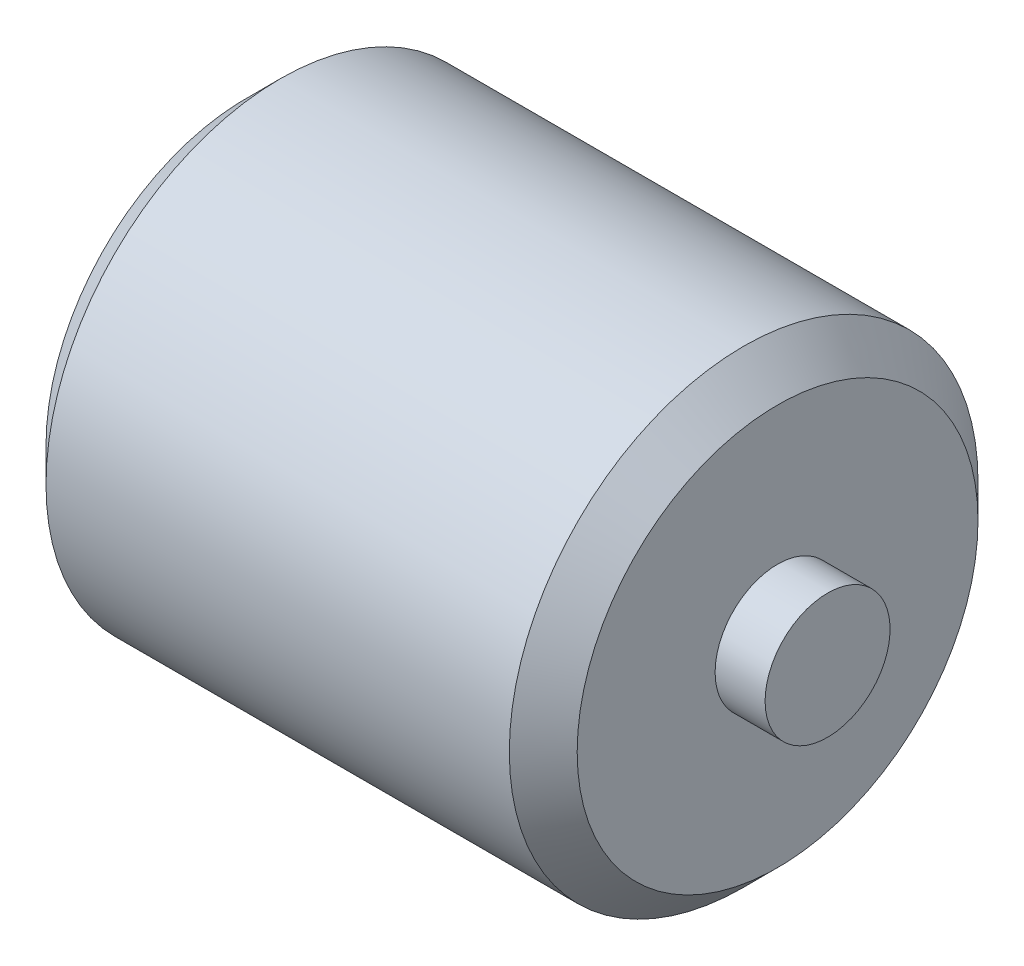
SolidWorks part; units mm, degrees
ref_plane "Alzado" through (0, 0, 0) normal (0, 0, 1) x (1, 0, 0)
ref_plane "Planta" through (0, 0, 0) normal (0, 1, 0) x (1, 0, 0)
ref_plane "Vista lateral" through (0, 0, 0) normal (1, 0, 0) x (0, 0, -1)
sketch "Croquis1" plane through (0, 0, 0) normal (0, 0, 1) x (1, 0, 0)
  line L0 (0, 0) -> (182, 0) construction
  line L1 (182, 0) -> (182, 10)
  line L2 (182, 10) -> (166, 10)
  line L3 (166, 10) -> (166, 60)
  line L4 (166, 60) -> (161, 65)
  line L5 (161, 65) -> (21, 65)
  line L6 (21, 65) -> (16, 60)
  line L7 (16, 60) -> (16, 10)
  line L8 (16, 10) -> (0, 10)
  line L9 (0, 10) -> (0, 0)
  dimension "D1" = 182
  dimension "D2" = 10
  dimension "D3" = 16
  dimension "D5" = 50
  dimension "D4" = 150
  dimension "D6" = 45
  dimension "D7" = 140
  dimension "D8" = 50
  dimension "D9" = 10
revolve "Revolución-Lámina1" add sketch "Croquis1" angle 360 about L0
equation "\"A\"= 10"
equation "\"B\"= 2"
equation "\"D1@Croquis1\"=((\"A\"*18)+\"B\")"
equation "\"D2@Croquis1\"=\"A\""
equation "\"D3@Croquis1\"=\"A\"+6"
equation "\"D5@Croquis1\"=\"A\"*5"
equation "\"D7@Croquis1\"=\"A\"*14"
equation "\"D8@Croquis1\"=\"D5@Croquis1\""
equation "\"D9@Croquis1\"=\"D2@Croquis1\""
